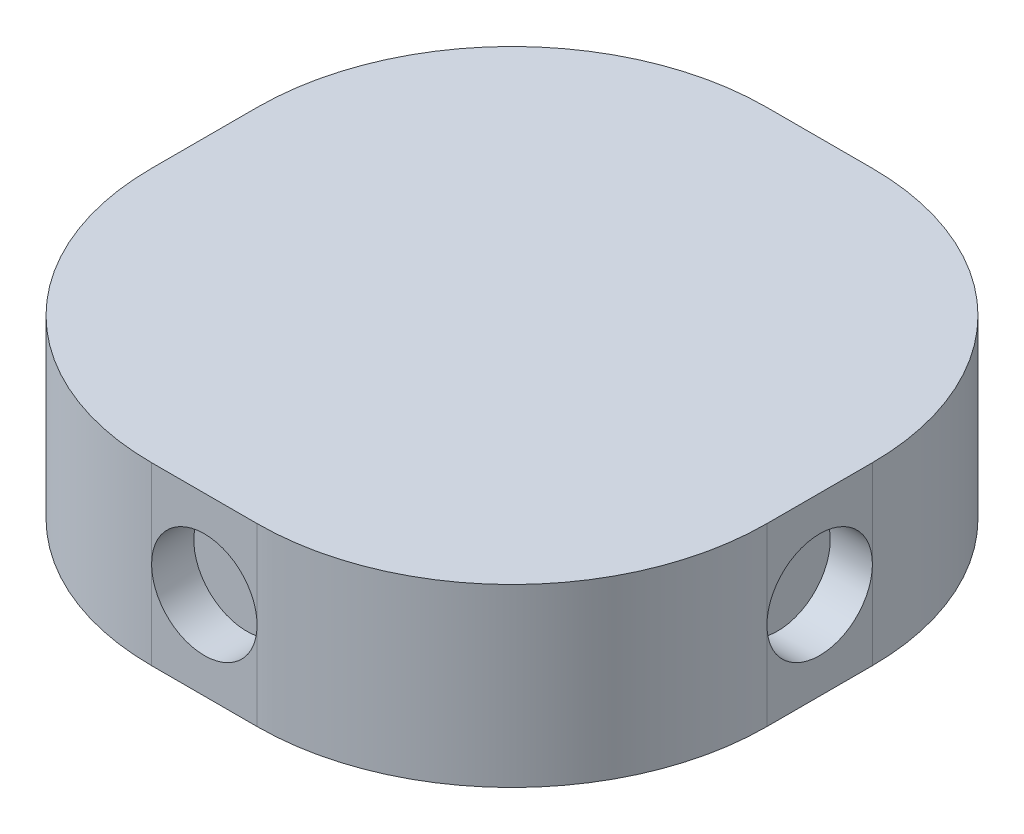
SolidWorks part; units mm, degrees
ref_plane "Front Plane" through (0, 0, 0) normal (0, 0, 1) x (1, 0, 0)
ref_plane "Top Plane" through (0, 0, 0) normal (0, 1, 0) x (1, 0, 0)
ref_plane "Right Plane" through (0, 0, 0) normal (1, 0, 0) x (0, 0, -1)
sketch "Sketch1" plane through (0, 0, 0) normal (0, 1, 0) x (1, 0, 0)
  line L1 (-128.0676, -163.7398) -> (-125.0676, -163.7398)
  line L2 (-135.3176, -156.4898) -> (-135.3176, -153.4898)
  line L3 (-128.0676, -146.2398) -> (-125.0676, -146.2398)
  line L4 (-117.8176, -156.4898) -> (-117.8176, -153.4898)
  arc A0 (-135.3176, -153.4898) -> (-128.0676, -146.2398) centre (-128.0676, -153.4898) cw
  arc A1 (-125.0676, -146.2398) -> (-117.8176, -153.4898) centre (-125.0676, -153.4898) cw
  arc A2 (-125.0676, -163.7398) -> (-117.8176, -156.4898) centre (-125.0676, -156.4898) ccw
  arc A3 (-128.0676, -163.7398) -> (-135.3176, -156.4898) centre (-128.0676, -156.4898) cw
  point P6 (-135.3176, -146.2398)
  point P11 (-117.8176, -163.7398)
  point P14 (-135.3176, -163.7398)
  dimension "D3" = 7.25
  dimension "D1" = 17.5
  dimension "D2" = 17.5
extrude "Boss-Extrude3" add sketch "Sketch1" along normal blind 5
sketch "Sketch3" plane through (0, 0, 146.2398) normal (0, 0, -1) x (-1, 0, 0)
  line L0 (125.0676, 0) -> (128.0676, 0) construction
  circle A0 centre (126.5676, 2.5) radius 1.5
  point P4 (126.5676, 0)
  dimension "D1" = 3
  dimension "D3" = 2.5
  dimension "D2" = 0
extrude "Cut-Extrude1" cut sketch "Sketch3" against normal blind 1.2
sketch "Sketch4" plane through (-117.8176, 0, 0) normal (1, 0, 0) x (0, 0, -1)
  line L0 (-156.4898, 0) -> (-153.4898, 0) construction
  line L2 (-156.4898, 5) -> (-153.4898, 5) construction
  circle A0 centre (-154.9898, 2.5) radius 1.5
  point P4 (-154.9898, 0)
  point P7 (-154.4091, 5)
  dimension "D1" = 3
  dimension "D2" = 2.5
  dimension "D3" = 2.5
extrude "Cut-Extrude2" cut sketch "Sketch4" against normal blind 1.2
sketch "Sketch5" plane through (-135.3176, 0, 0) normal (-1, 0, 0) x (0, 0, 1)
  line L0 (153.4898, 0) -> (156.4898, 0) construction
  line L1 (153.4898, 5) -> (156.4898, 5) construction
  circle A0 centre (154.9898, 2.5) radius 1.5
  point P6 (154.9898, 5)
  dimension "D1" = 3
  dimension "D2" = 2.5
  dimension "D3" = 0
extrude "Cut-Extrude3" cut sketch "Sketch5" against normal blind 1.2
sketch "Sketch6" plane through (0, 0, 163.7398) normal (0, 0, 1) x (1, 0, 0)
  line L0 (-128.0676, 5) -> (-125.0676, 5) construction
  line L1 (-128.0676, 0) -> (-125.0676, 0) construction
  circle A0 centre (-126.5676, 2.5) radius 1.5
  point P6 (-126.5676, 0)
  dimension "D1" = 3
  dimension "D2" = 2.5
  dimension "D3" = 0
extrude "Cut-Extrude4" cut sketch "Sketch6" against normal blind 1.2
